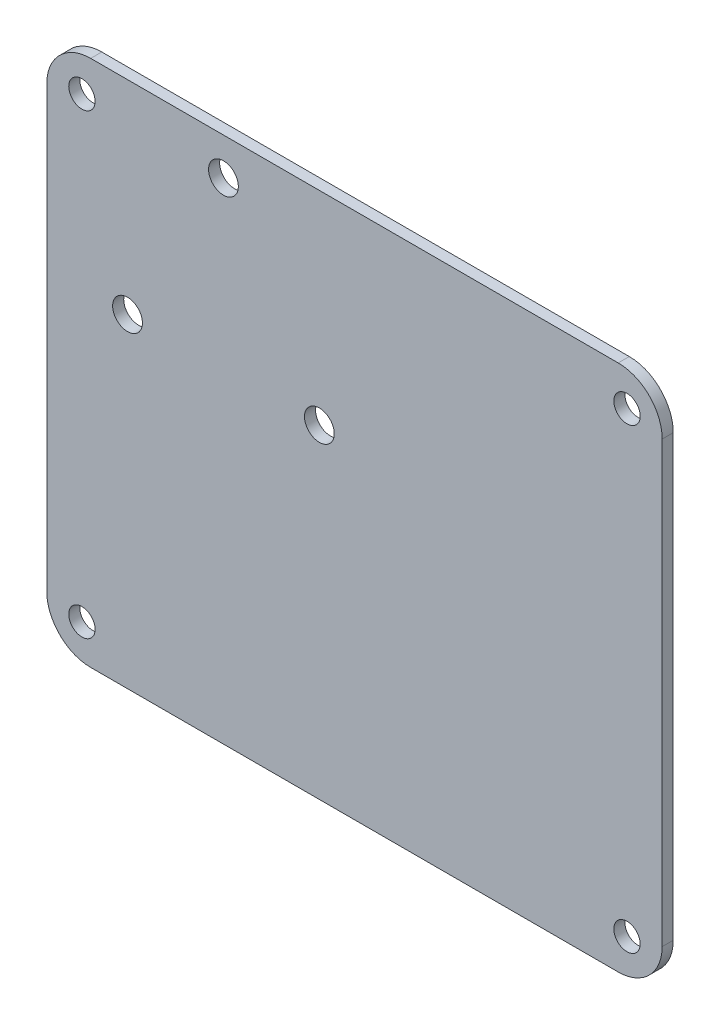
SolidWorks part; units mm, degrees
ref_plane "Front Plane" through (0, 0, 0) normal (0, 0, 1) x (1, 0, 0)
ref_plane "Top Plane" through (0, 0, 0) normal (0, 1, 0) x (1, 0, 0)
ref_plane "Right Plane" through (0, 0, 0) normal (1, 0, 0) x (0, 0, -1)
sketch "Sketch1" plane through (0, 0, 0) normal (0, 0, 1) x (1, 0, 0)
  line L1 (-15.4905, -8.0369) -> (73.4095, -8.0369)
  line L2 (-15.4905, -8.0369) -> (-15.4905, 68.1631)
  line L3 (-15.4905, 68.1631) -> (73.4095, 68.1631)
  line L4 (73.4095, -8.0369) -> (73.4095, 68.1631)
  line L8 (25.8595, 61.8131) -> (-9.1405, 61.8131) construction
  line L9 (-9.1405, 61.8131) -> (-9.1405, 36.8131) construction
  dimension "D1" = 76.2
  dimension "D2" = 88.9
  dimension "D3" = 6.35
  dimension "D4" = 6.35
extrude "Boss-Extrude1" add sketch "Sketch1" along normal blind 1.6
sketch "Sketch2" plane through (0, 0, 0) normal (0, 0, -1) x (-1, 0, 0)
  circle A8 centre (-23.8907, 38.79) radius 2.15 construction
  circle A9 centre (3.8221, 38.79) radius 2.15 construction
  circle A10 centre (-10.0343, 62.79) radius 2.15 construction
  circle A11 centre (-23.8907, 38.79) radius 2.15
  circle A12 centre (3.8221, 38.79) radius 2.15
  circle A13 centre (-10.0343, 62.79) radius 2.15
extrude "Cut-Extrude1" cut sketch "Sketch2" against normal through all
sketch "Sketch4" plane through (0, 0, 0) normal (0, 0, -1) x (-1, 0, 0)
  line L0 (-28.9595, 68.1631) -> (-28.9595, -8.0369) construction
  line L1 (-73.4095, 68.1631) -> (15.4905, 68.1631) construction
  line L2 (15.4905, -8.0369) -> (-73.4095, -8.0369) construction
  line L3 (-73.4095, 30.0631) -> (15.4905, 30.0631) construction
  line L4 (-73.4095, -8.0369) -> (-73.4095, 68.1631) construction
  line L5 (15.4905, 68.1631) -> (15.4905, -8.0369) construction
  circle A0 centre (10.4105, 63.0831) radius 1.905
  circle A1 centre (-68.3295, 63.0831) radius 1.905
  circle A2 centre (-68.3295, -2.9569) radius 1.905
  circle A3 centre (10.4105, -2.9569) radius 1.905
  dimension "D1" = 3.81
  dimension "D2" = 5.08
  dimension "D3" = 5.08
extrude "Cut-Extrude2" cut sketch "Sketch4" against normal through all
fillet "Fillet1" radius 6.35 4 edges at (73.4095, 68.1631, 0.8) (73.4095, -8.0369, 0.8) (-15.4905, -8.0369, 0.8) (-15.4905, 68.1631, 0.8)
sketch "Sketch5" plane through (0, 0, 1.6) normal (0, 0, 1) x (1, 0, 0)
  line L0 (-15.4905, 61.8131) -> (-15.4905, -1.6869) construction
  line L1 (-9.1405, -8.0369) -> (67.0595, -8.0369) construction
  line L2 (67.0595, 68.1631) -> (-9.1405, 68.1631) construction
  circle A0 centre (-10.4105, -2.9569) radius 1.905 construction
  circle A3 centre (-10.4105, -2.9569) radius 1.905
  circle A4 centre (15.8595, 42.8131) radius 3 construction
  circle A7 centre (15.8595, 55.8131) radius 3 construction
  point P0 (-10.4105, 63.0831)
  point P1 (-10.4105, -2.9569)
  point P3 (68.3295, -2.9569)
  point P5 (68.3295, 63.0831)
  point P7 (10.0343, 62.79)
  point P9 (0, 0)
  point P11 (0, 0)
  point P15 (-15.4905, -8.0369)
  point P17 (0, 0)
  point P30 (-0.3157, 68.1631)
  dimension "D10" = 3.81
  dimension "D2" = 5.08
  dimension "D3" = 5.3731
  dimension "D5" = 71.12
  dimension "D6" = 10.35
  dimension "D8" = 68.6452
  dimension "D12" = 16.1752
  dimension "D13" = 25.35
  dimension "D14" = 12.35
ref_plane "Plane1" through (28.9595, 0, 0) normal (-1, 0, 0) x (0, 0, 1)
